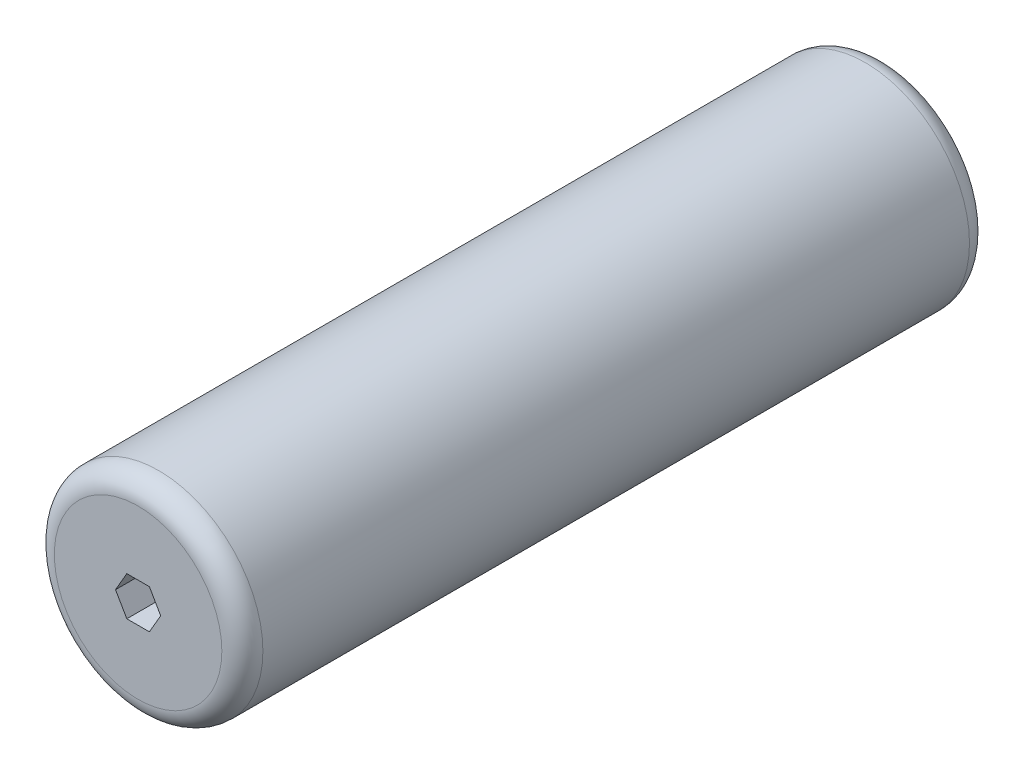
SolidWorks part; units mm, degrees
ref_plane "Front Plane" through (0, 0, 0) normal (0, 0, 1) x (1, 0, 0)
ref_plane "Top Plane" through (0, 0, 0) normal (0, 1, 0) x (1, 0, 0)
ref_plane "Right Plane" through (0, 0, 0) normal (1, 0, 0) x (0, 0, -1)
sketch "Sketch1" plane through (0, 0, 0) normal (0, 0, 1) x (1, 0, 0)
  circle A0 centre (0, 0) radius 25.4
  dimension "D1" = 50.8
extrude "Boss-Extrude1" add sketch "Sketch1" along normal blind 182.118
sketch "Sketch2" plane through (0, 0, 182.118) normal (0, 0, 1) x (1, 0, 0)
  line L1 (5.4993, 0) -> (2.7496, 4.7625)
  line L2 (2.7496, 4.7625) -> (-2.7496, 4.7625)
  line L3 (-2.7496, 4.7625) -> (-5.4993, 0)
  line L4 (-5.4993, 0) -> (-2.7496, -4.7625)
  line L5 (-2.7496, -4.7625) -> (2.7496, -4.7625)
  line L6 (2.7496, -4.7625) -> (5.4993, 0)
  circle A0 centre (0, 0) radius 4.7625 construction
extrude "Cut-Extrude1" cut sketch "Sketch2" against normal through all
fillet "Fillet1" radius 5 2 edges at (25.4, 0, 0) (25.4, 0, 182.118)
